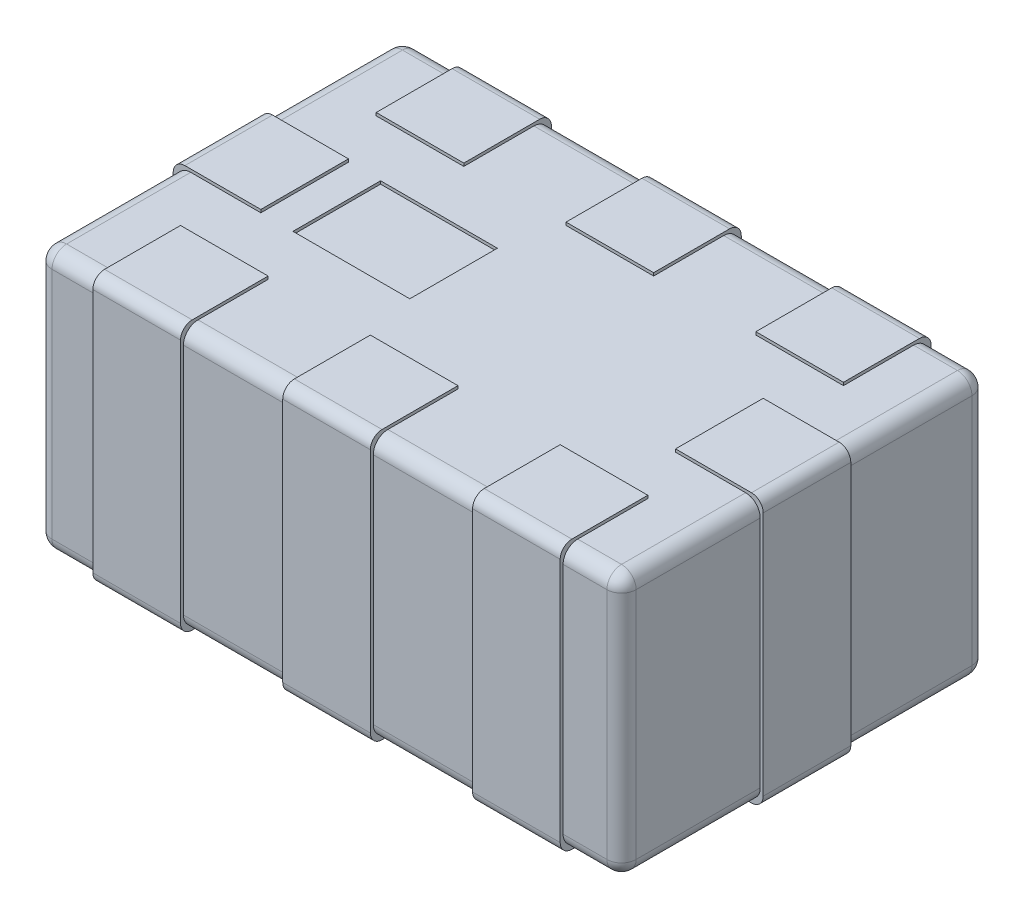
SolidWorks part; units mm, degrees
ref_plane "Front Plane" through (0, 0, 0) normal (0, 0, 1) x (1, 0, 0)
ref_plane "Top Plane" through (0, 0, 0) normal (0, 1, 0) x (1, 0, 0)
ref_plane "Right Plane" through (0, 0, 0) normal (1, 0, 0) x (0, 0, -1)
sketch "Sketch1" plane through (0, 0, 0) normal (0, 1, 0) x (1, 0, 0)
  line L1 (-1, 0.625) -> (1, 0.625)
  line L2 (-1, 0.625) -> (-1, -0.625)
  line L3 (-1, -0.625) -> (1, -0.625)
  line L4 (1, 0.625) -> (1, -0.625)
  line L5 (-1, 0.625) -> (1, -0.625) construction
  line L6 (-1, -0.625) -> (1, 0.625) construction
  point P0 (0, 0)
  dimension "D1" = 2
  dimension "D2" = 1.25
extrude "Boss-Extrude1" add sketch "Sketch1" along normal blind 0.9
fillet "Fillet1" radius 0.05 12 edges at (1, 0.45, 0.625) (-1, 0.45, 0.625) (1, 0.9, 0) (0, 0.9, 0.625) (0, 0, 0.625) (1, 0, 0) (1, 0.45, -0.625) (-1, 0.9, 0) (0, 0.9, -0.625) (-1, 0.45, -0.625) (-1, 0, 0) (0, 0, -0.625)
sketch "Sketch2" plane through (0, 0, 0) normal (0, -1, 0) x (1, 0, 0)
  line L0 (-1, 0) -> (1, 0) construction
  line L1 (-1.01, 0.15) -> (-0.71, 0.15)
  line L2 (-1.01, 0.15) -> (-1.01, -0.15)
  line L3 (-1.01, -0.15) -> (-0.71, -0.15)
  line L4 (-0.71, 0.15) -> (-0.71, -0.15)
  line L5 (-1, -0.625) -> (-1, 0.625) construction
  line L6 (1, 0.625) -> (1, -0.625) construction
  line L7 (0, 0) -> (0, 0.625) construction
  line L8 (-1, 0.625) -> (1, 0.625) construction
  line L9 (1.01, -0.15) -> (0.71, -0.15)
  line L10 (0.71, 0.15) -> (0.71, -0.15)
  line L11 (1.01, 0.15) -> (0.71, 0.15)
  line L12 (1.01, 0.15) -> (1.01, -0.15)
  line L13 (-0.8, 0.635) -> (-0.5, 0.635)
  line L14 (-0.8, 0.635) -> (-0.8, 0.335)
  line L15 (-0.8, 0.335) -> (-0.5, 0.335)
  line L16 (-0.5, 0.635) -> (-0.5, 0.335)
  line L17 (-0.15, 0.635) -> (0.15, 0.635)
  line L18 (-0.15, 0.635) -> (-0.15, 0.335)
  line L19 (-0.15, 0.335) -> (0.15, 0.335)
  line L20 (0.15, 0.635) -> (0.15, 0.335)
  line L21 (0.8, 0.635) -> (0.8, 0.335)
  line L22 (0.8, 0.335) -> (0.5, 0.335)
  line L23 (0.5, 0.635) -> (0.5, 0.335)
  line L24 (0.8, 0.635) -> (0.5, 0.635)
  line L25 (0.8, -0.635) -> (0.5, -0.635)
  line L26 (0.5, -0.635) -> (0.5, -0.335)
  line L27 (0.8, -0.335) -> (0.5, -0.335)
  line L28 (0.8, -0.635) -> (0.8, -0.335)
  line L29 (-0.15, -0.635) -> (-0.15, -0.335)
  line L30 (-0.15, -0.335) -> (0.15, -0.335)
  line L31 (0.15, -0.635) -> (0.15, -0.335)
  line L32 (-0.15, -0.635) -> (0.15, -0.635)
  line L33 (-0.8, -0.635) -> (-0.8, -0.335)
  line L34 (-0.8, -0.335) -> (-0.5, -0.335)
  line L35 (-0.5, -0.635) -> (-0.5, -0.335)
  line L36 (-0.8, -0.635) -> (-0.5, -0.635)
  point P23 (-0.65, 0.635)
  point P28 (0, 0.635)
  point P29 (0, 0)
  dimension "D1" = 0.3
  dimension "D2" = 0.3
  dimension "D3" = 0.01
  dimension "D4" = 0.01
  dimension "D5" = 0.35
extrude "Boss-Extrude2" add sketch "Sketch2" along normal blind 0.01
sketch "Sketch4" plane through (0, 0, 0) normal (0, -1, 0) x (1, 0, 0)
  line L4 (-0.71, 0.15) -> (-1.01, 0.15)
  line L5 (-0.71, -0.15) -> (-0.71, 0.15)
  line L6 (-1.01, -0.15) -> (-0.71, -0.15)
  line L7 (-1.01, 0.15) -> (-1.01, -0.15)
  line L8 (-0.71, 0.15) -> (-1.01, 0.15)
  line L9 (-0.71, -0.15) -> (-0.71, 0.15)
  line L10 (-1.01, -0.15) -> (-0.71, -0.15)
  line L11 (-1.01, 0.15) -> (-1.01, -0.15)
  line L12 (0.15, 0.635) -> (-0.15, 0.635)
  line L13 (0.15, 0.335) -> (0.15, 0.635)
  line L14 (-0.15, 0.335) -> (0.15, 0.335)
  line L15 (-0.15, 0.635) -> (-0.15, 0.335)
  line L16 (0.15, 0.635) -> (-0.15, 0.635)
  line L17 (0.15, 0.335) -> (0.15, 0.635)
  line L18 (-0.15, 0.335) -> (0.15, 0.335)
  line L19 (-0.15, 0.635) -> (-0.15, 0.335)
  line L20 (-0.5, 0.635) -> (-0.8, 0.635)
  line L21 (-0.5, 0.335) -> (-0.5, 0.635)
  line L22 (-0.8, 0.335) -> (-0.5, 0.335)
  line L23 (-0.8, 0.635) -> (-0.8, 0.335)
  line L24 (-0.5, 0.635) -> (-0.8, 0.635)
  line L25 (-0.5, 0.335) -> (-0.5, 0.635)
  line L26 (-0.8, 0.335) -> (-0.5, 0.335)
  line L27 (-0.8, 0.635) -> (-0.8, 0.335)
  line L28 (0.71, 0.15) -> (0.71, -0.15)
  line L29 (1.01, 0.15) -> (0.71, 0.15)
  line L30 (1.01, -0.15) -> (1.01, 0.15)
  line L31 (0.71, -0.15) -> (1.01, -0.15)
  line L32 (0.71, 0.15) -> (0.71, -0.15)
  line L33 (1.01, 0.15) -> (0.71, 0.15)
  line L34 (1.01, -0.15) -> (1.01, 0.15)
  line L35 (0.71, -0.15) -> (1.01, -0.15)
  line L36 (-0.8, -0.335) -> (-0.8, -0.635)
  line L37 (-0.5, -0.335) -> (-0.8, -0.335)
  line L38 (-0.5, -0.635) -> (-0.5, -0.335)
  line L39 (-0.8, -0.635) -> (-0.5, -0.635)
  line L40 (-0.8, -0.335) -> (-0.8, -0.635)
  line L41 (-0.5, -0.335) -> (-0.8, -0.335)
  line L42 (-0.5, -0.635) -> (-0.5, -0.335)
  line L43 (-0.8, -0.635) -> (-0.5, -0.635)
  line L44 (-0.15, -0.335) -> (-0.15, -0.635)
  line L45 (0.15, -0.335) -> (-0.15, -0.335)
  line L46 (0.15, -0.635) -> (0.15, -0.335)
  line L47 (-0.15, -0.635) -> (0.15, -0.635)
  line L48 (-0.15, -0.335) -> (-0.15, -0.635)
  line L49 (0.15, -0.335) -> (-0.15, -0.335)
  line L50 (0.15, -0.635) -> (0.15, -0.335)
  line L51 (-0.15, -0.635) -> (0.15, -0.635)
  line L52 (0.5, -0.635) -> (0.8, -0.635)
  line L53 (0.5, -0.335) -> (0.5, -0.635)
  line L54 (0.8, -0.335) -> (0.5, -0.335)
  line L55 (0.8, -0.635) -> (0.8, -0.335)
  line L56 (0.5, -0.635) -> (0.8, -0.635)
  line L57 (0.5, -0.335) -> (0.5, -0.635)
  line L58 (0.8, -0.335) -> (0.5, -0.335)
  line L59 (0.8, -0.635) -> (0.8, -0.335)
  line L60 (0.5, 0.635) -> (0.5, 0.335)
  line L61 (0.8, 0.635) -> (0.5, 0.635)
  line L62 (0.8, 0.335) -> (0.8, 0.635)
  line L63 (0.5, 0.335) -> (0.8, 0.335)
  line L64 (0.5, 0.635) -> (0.5, 0.335)
  line L65 (0.8, 0.635) -> (0.5, 0.635)
  line L66 (0.8, 0.335) -> (0.8, 0.635)
  line L67 (0.5, 0.335) -> (0.8, 0.335)
  dimension "D1" = 0
  dimension "D2" = 0
  dimension "D3" = 0
  dimension "D4" = 0
  dimension "D5" = 0
  dimension "D6" = 0
  dimension "D7" = 0
  dimension "D8" = 0
extrude "Boss-Extrude3" add sketch "Sketch4" against normal blind 0.91
sketch "Sketch3" plane through (0, 0.9, 0) normal (0, 1, 0) x (1, 0, 0)
  line L0 (-1.01, 0) -> (1, 0) construction
  line L1 (-1, -0.575) -> (-1, -0.15) construction
  line L3 (-1.01, -0.15) -> (-1.01, 0.15) construction
  line L4 (-0.6, 0.15) -> (-0.2, 0.15)
  line L5 (-0.6, 0.15) -> (-0.6, -0.15)
  line L6 (-0.6, -0.15) -> (-0.2, -0.15)
  line L7 (-0.2, 0.15) -> (-0.2, -0.15)
  point P4 (-1.01, 0)
  point P10 (-1.01, 0.3625)
  dimension "D1" = 0.4
  dimension "D2" = 0.4
  dimension "D3" = 0.3
extrude "Cut-Extrude1" cut sketch "Sketch3" against normal blind 0.01
fillet "Fillet2" radius 0.04 16 edges at (-1.01, -0.01, 0) (-0.65, -0.01, -0.635) (0, -0.01, -0.635) (0.65, -0.01, -0.635) (1.01, -0.01, 0) (0.65, -0.01, 0.635) (0, -0.01, 0.635) (-0.65, -0.01, 0.635) (1.01, 0.91, 0) (0.65, 0.91, -0.635) (0.65, 0.91, 0.635) (0, 0.91, 0.635) (0, 0.91, -0.635) (-0.65, 0.91, -0.635) (-0.65, 0.91, 0.635) (-1.01, 0.91, 0)
